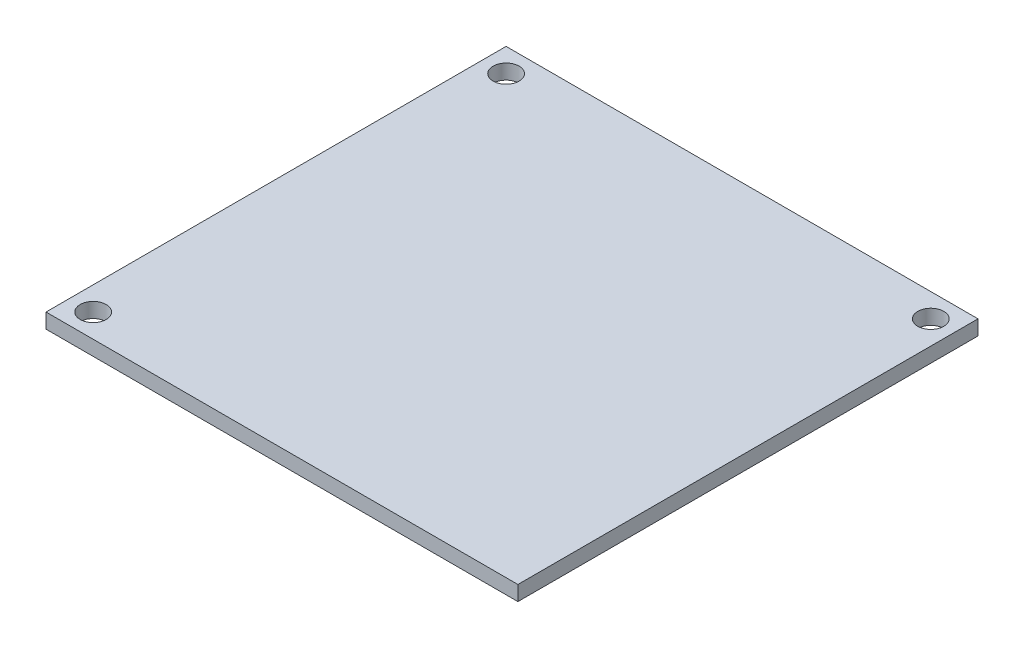
SolidWorks part; units mm, degrees
ref_plane "Front Plane" through (0, 0, 0) normal (0, 0, 1) x (1, 0, 0)
ref_plane "Top Plane" through (0, 0, 0) normal (0, 1, 0) x (1, 0, 0)
ref_plane "Right Plane" through (0, 0, 0) normal (1, 0, 0) x (0, 0, -1)
sketch "Sketch2" plane through (0, 0, 0) normal (0, 1, 0) x (1, 0, 0)
  line L1 (25.4, -24.765) -> (-25.4, -24.765)
  line L2 (25.4, -24.765) -> (25.4, 24.765)
  line L3 (25.4, 24.765) -> (-25.4, 24.765)
  line L4 (-25.4, -24.765) -> (-25.4, 24.765)
  line L5 (25.4, -24.765) -> (-25.4, 24.765) construction
  line L6 (25.4, 24.765) -> (-25.4, -24.765) construction
  point P0 (0, 0)
  dimension "D1" = 49.53
  dimension "D2" = 50.8
extrude "Boss-Extrude1" add sketch "Sketch2" along normal blind 1.6
sketch "Sketch3" plane through (0, 1.6, 0) normal (0, 1, 0) x (1, 0, 0)
  line L0 (-25.4, 24.765) -> (-25.4, -24.765) construction
  line L1 (25.4, -24.765) -> (25.4, 24.765) construction
  line L2 (25.4, 24.765) -> (-25.4, 24.765) construction
  line L3 (-25.4, -24.765) -> (25.4, -24.765) construction
  circle A0 centre (-22.86, 22.225) radius 1.4
  circle A1 centre (22.86, 22.225) radius 1.4
  circle A2 centre (-22.86, -22.225) radius 1.4
  dimension "D1" = 2.54
  dimension "D3" = 2.54
  dimension "D4" = 2.54
  dimension "D2" = 2.54
extrude "Cut-Extrude1" cut sketch "Sketch3" against normal blind 1.6
